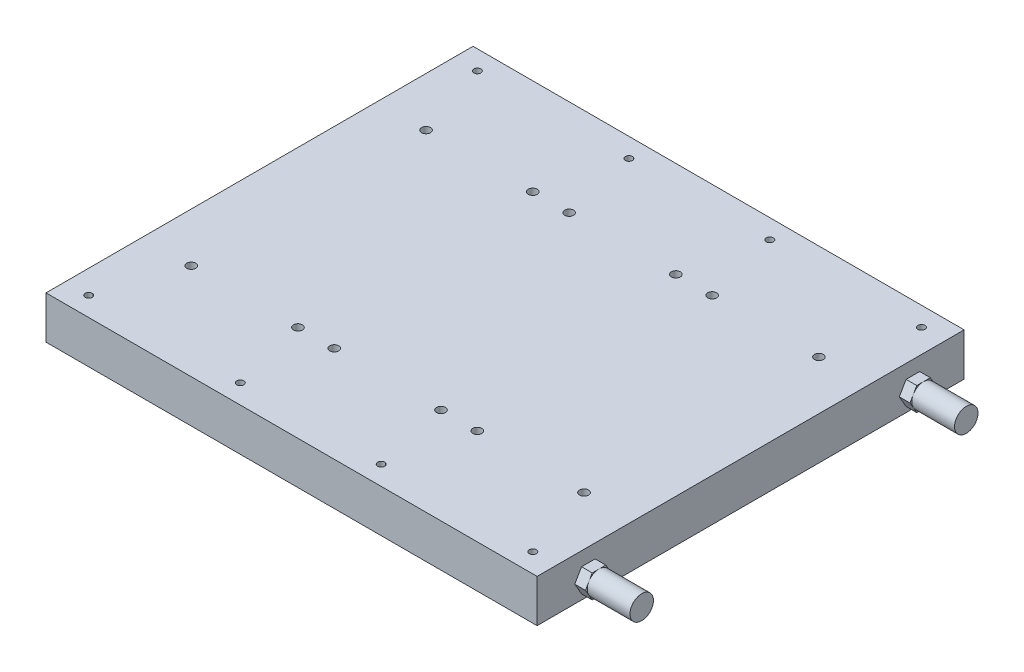
SolidWorks part; units mm, degrees
ref_plane "Płaszczyzna przednia" through (0, 0, 0) normal (0, 0, 1) x (1, 0, 0)
ref_plane "Płaszczyzna górna" through (0, 0, 0) normal (0, 1, 0) x (1, 0, 0)
ref_plane "Płaszczyzna prawa" through (0, 0, 0) normal (1, 0, 0) x (0, 0, -1)
sketch "Szkic1" plane through (0, 0, 0) normal (0, 1, 0) x (1, 0, 0)
  line L1 (-115, -100) -> (115, -100)
  line L2 (-115, -100) -> (-115, 100)
  line L3 (-115, 100) -> (115, 100)
  line L4 (115, -100) -> (115, 100)
  line L5 (-115, -100) -> (115, 100) construction
  line L6 (-115, 100) -> (115, -100) construction
  point P0 (0, 0)
  dimension "D1" = 200
  dimension "D2" = 230
extrude "Dodanie-wyciągnięcie1" add sketch "Szkic1" along normal blind 20
sketch "Szkic5" plane through (0, 20, 0) normal (0, 1, 0) x (1, 0, 0)
  line L1 (-42, -55) -> (-92, -55)
  line L2 (-42, -55) -> (-42, 55)
  line L3 (-42, 55) -> (-92, 55)
  line L4 (-92, -55) -> (-92, 55)
  line L5 (-42, -55) -> (-92, 55) construction
  line L6 (-42, 55) -> (-92, -55) construction
  line L7 (25, -55) -> (-25, -55)
  line L8 (25, -55) -> (25, 55)
  line L9 (25, 55) -> (-25, 55)
  line L10 (-25, -55) -> (-25, 55)
  line L11 (25, -55) -> (-25, 55) construction
  line L12 (25, 55) -> (-25, -55) construction
  line L13 (42, -55) -> (92, -55)
  line L14 (42, -55) -> (42, 55)
  line L15 (42, 55) -> (92, 55)
  line L16 (92, -55) -> (92, 55)
  line L17 (42, -55) -> (92, 55) construction
  line L18 (42, 55) -> (92, -55) construction
  point P0 (-67, 0)
  point P5 (0, 0)
  point P11 (67, 0)
  dimension "D1" = 50
  dimension "D2" = 50
  dimension "D3" = 50
  dimension "D4" = 110
  dimension "D5" = 17
  dimension "D6" = 17
hole_wizard "Otwór gwintowany M52" positions "Szkic 3D2" profile "Szkic6" tap size "M5" standard "ISO"
sketch3d "Szkic 3D2"
  point P0 (-92, 20, -55)
  point P3 (-42, 20, -55)
  point P6 (-25, 20, -55)
  point P9 (25, 20, -55)
  point P12 (25, 20, 55)
  point P15 (-25, 20, 55)
  point P18 (-42, 20, 55)
  point P21 (-92, 20, 55)
  point P24 (42, 20, 55)
  point P27 (42, 20, -55)
  point P30 (92, 20, -55)
  point P33 (92, 20, 55)
sketch "Szkic6" plane through (-92, 20, -55) normal (1, 0, 0) x (0, 0, 1)
  line L0 (0, 0) -> (0, 15.2618)
  line L1 (0, 15.2618) -> (2.1, 14)
  line L2 (2.1, 14) -> (2.1, 0)
  line L5 (2.1, 0) -> (0, 0)
  line L10 (0, 15.2618) -> (-2.1, 14) construction
  line L11 (0, -6.35) -> (0, 107.95) construction
  dimension "Średnica wiertła gwintu" = 4.2
  dimension "Głębokość otworu gwintowanego" = 14
  dimension "Kąt wiertła" = 118
cosmetic thread "Gwint otworu13" parameters "D1"=10, "D2"=5
cosmetic thread "Gwint otworu14" parameters "D1"=10, "D2"=5
cosmetic thread "Gwint otworu15" parameters "D1"=10, "D2"=5
cosmetic thread "Gwint otworu16" parameters "D1"=10, "D2"=5
cosmetic thread "Gwint otworu17" parameters "D1"=10, "D2"=5
cosmetic thread "Gwint otworu18" parameters "D1"=10, "D2"=5
cosmetic thread "Gwint otworu19" parameters "D1"=10, "D2"=5
cosmetic thread "Gwint otworu20" parameters "D1"=10, "D2"=5
cosmetic thread "Gwint otworu21" parameters "D1"=10, "D2"=5
cosmetic thread "Gwint otworu22" parameters "D1"=10, "D2"=5
cosmetic thread "Gwint otworu23" parameters "D1"=10, "D2"=5
cosmetic thread "Gwint otworu24" parameters "D1"=10, "D2"=5
sketch "Szkic7" plane through (0, 20, 0) normal (0, 1, 0) x (1, 0, 0)
  line L1 (-33, -91) -> (33, -91)
  line L2 (-33, -91) -> (-33, 91)
  line L3 (-33, 91) -> (33, 91)
  line L4 (33, -91) -> (33, 91)
  line L5 (-33, -91) -> (33, 91) construction
  line L6 (-33, 91) -> (33, -91) construction
  line L7 (-104, -91) -> (104, -91)
  line L8 (-104, -91) -> (-104, 91)
  line L9 (-104, 91) -> (104, 91)
  line L10 (104, -91) -> (104, 91)
  line L11 (-104, -91) -> (104, 91) construction
  line L12 (-104, 91) -> (104, -91) construction
  point P0 (0, 0)
  point P6 (0, 0)
  dimension "D1" = 182
  dimension "D2" = 66
  dimension "D3" = 71
hole_wizard "Otwór gwintowany M41" positions "Szkic 3D3" profile "Szkic8" tap size "M4" standard "ISO"
sketch3d "Szkic 3D3"
  point P0 (-104, 20, -91)
  point P3 (-33, 20, -91)
  point P6 (33, 20, -91)
  point P9 (104, 20, -91)
  point P12 (104, 20, 91)
  point P15 (33, 20, 91)
  point P18 (-33, 20, 91)
  point P21 (-104, 20, 91)
sketch "Szkic8" plane through (-104, 20, -91) normal (1, 0, 0) x (0, 0, 1)
  line L0 (0, 0) -> (0, 12.4914)
  line L1 (0, 12.4914) -> (1.65, 11.5)
  line L2 (1.65, 11.5) -> (1.65, 0)
  line L5 (1.65, 0) -> (0, 0)
  line L10 (0, 12.4914) -> (-1.65, 11.5) construction
  line L11 (0, -6.35) -> (0, 107.95) construction
  dimension "Średnica wiertła gwintu" = 3.3
  dimension "Głębokość otworu gwintowanego" = 11.5
  dimension "Kąt wiertła" = 118
cosmetic thread "Gwint otworu25" parameters "D1"=8, "D2"=4
cosmetic thread "Gwint otworu26" parameters "D1"=8, "D2"=4
cosmetic thread "Gwint otworu27" parameters "D1"=8, "D2"=4
cosmetic thread "Gwint otworu28" parameters "D1"=8, "D2"=4
cosmetic thread "Gwint otworu29" parameters "D1"=8, "D2"=4
cosmetic thread "Gwint otworu30" parameters "D1"=8, "D2"=4
cosmetic thread "Gwint otworu31" parameters "D1"=8, "D2"=4
cosmetic thread "Gwint otworu32" parameters "D1"=8, "D2"=4
sketch "Szkic9" plane through (115, 0, 0) normal (1, 0, 0) x (0, 0, -1)
  line L0 (-76, 8) -> (76, 8)
  line L1 (-100, 0) -> (100, 0) construction
  line L3 (-69.6491, 8) -> (-72.8246, 13.5)
  line L4 (-72.8246, 13.5) -> (-79.1754, 13.5)
  line L5 (-79.1754, 13.5) -> (-82.3509, 8)
  line L6 (-82.3509, 8) -> (-79.1754, 2.5)
  line L7 (-79.1754, 2.5) -> (-72.8246, 2.5)
  line L8 (-72.8246, 2.5) -> (-69.6491, 8)
  line L9 (69.6491, 8) -> (72.8246, 2.5)
  line L10 (72.8246, 2.5) -> (79.1754, 2.5)
  line L11 (79.1754, 2.5) -> (82.3509, 8)
  line L12 (82.3509, 8) -> (79.1754, 13.5)
  line L13 (79.1754, 13.5) -> (72.8246, 13.5)
  line L14 (72.8246, 13.5) -> (69.6491, 8)
  circle A0 centre (-76, 8) radius 5.5 construction
  circle A1 centre (76, 8) radius 5.5 construction
  dimension "D1" = 152
  dimension "D2" = 8
  dimension "D3" = 76
  dimension "D4" = 11
  dimension "D5" = 11
  dimension "D6" = 5.5
  dimension "D7" = 5.5
extrude "Dodanie-wyciągnięcie2" add sketch "Szkic9" along normal blind 5
sketch "Szkic10" plane through (120, 0, 0) normal (1, 0, 0) x (0, 0, -1)
  line L0 (-79.1754, 2.5) -> (-72.8246, 2.5) construction
  line L1 (-69.6491, 8) -> (-72.8246, 13.5) construction
  line L2 (-82.3509, 8) -> (-79.1754, 2.5) construction
  line L4 (79.1754, 13.5) -> (72.8246, 13.5) construction
  line L5 (79.1754, 2.5) -> (82.3509, 8) construction
  line L6 (72.8246, 13.5) -> (69.6491, 8) construction
  circle A0 centre (76, 8) radius 5.5
  circle A1 centre (-76, 8) radius 5.5
extrude "Dodanie-wyciągnięcie3" add sketch "Szkic10" along normal blind 20
